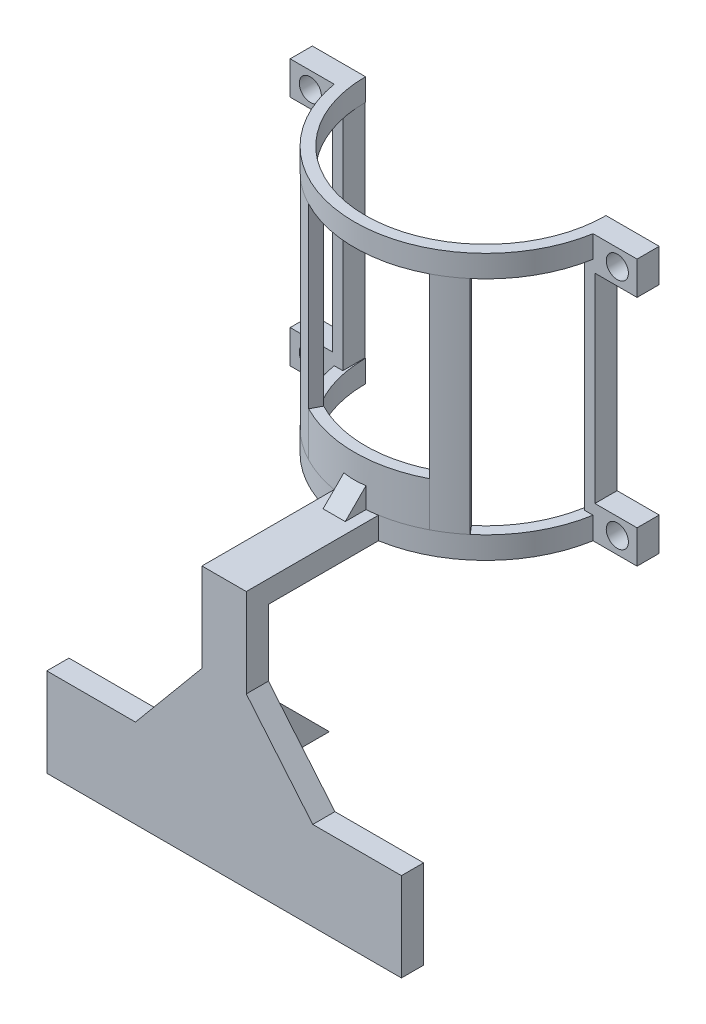
SolidWorks part; units mm, degrees
ref_plane "前视基准面" through (0, 0, 0) normal (0, 0, 1) x (1, 0, 0)
ref_plane "上视基准面" through (0, 0, 0) normal (0, 1, 0) x (1, 0, 0)
ref_plane "右视基准面" through (0, 0, 0) normal (1, 0, 0) x (0, 0, -1)
sketch "草图1" plane through (0, 0, 0) normal (0, 1, 0) x (1, 0, 0)
  line L0 (-118.5, 0) -> (-108.5, 0)
  line L1 (108.5, 0) -> (118.5, 0)
  arc A1 (-118.5, 0) -> (118.5, 0) centre (0, 0) ccw
  arc A2 (-108.5, 0) -> (108.5, 0) centre (0, 0) ccw
extrude "凸台-拉伸1" add sketch "草图1" along normal blind 20
ref_plane "基准面1" through (0, 0, 216.11) normal (0, 0, 1) x (1, 0, 0)
sketch "草图3" plane through (0, 0, 216.11) normal (0, 0, 1) x (1, 0, 0)
  line L0 (0, 0) -> (20, 0)
  line L2 (-118.5, 0) -> (118.5, 0) construction
  line L4 (20, 0) -> (20, 20)
  line L5 (118.5, 20) -> (-118.5, 20) construction
  line L6 (20, 20) -> (-20, 20)
  line L7 (-20, 20) -> (-20, 0)
  line L8 (-20, 0) -> (0, 0)
extrude "凸台-拉伸2" add sketch "草图3" against normal up to next
sketch "草图12" plane through (0, 0, 0) normal (0, 0, 1) x (1, 0, 0)
  line L0 (-109, 0) -> (-156.5, 0)
  line L1 (-156.5, 0) -> (-156.5, 30)
  line L2 (-156.5, 30) -> (-118.5, 30)
  line L3 (-109, 240) -> (-109, 0)
  line L4 (-109, 240) -> (-156.5, 240)
  line L5 (-156.5, 240) -> (-156.5, 210)
  line L6 (-118.5, 30) -> (-118.5, 210)
  line L7 (-118.5, 210) -> (-156.5, 210)
  line L8 (156.5, 0) -> (109, 0)
  line L10 (156.5, 0) -> (156.5, 30)
  line L11 (156.5, 30) -> (118.5, 30)
  line L12 (118.5, 30) -> (118.5, 210)
  line L13 (118.5, 210) -> (156.5, 210)
  line L14 (156.5, 210) -> (156.5, 240)
  line L15 (156.5, 240) -> (109, 240)
  line L17 (109, 240) -> (109, 0)
extrude "凸台-拉伸7" add sketch "草图12" along normal blind 20
sketch "草图13" plane through (0, 0, 0) normal (0, 0, -1) x (-1, 0, 0)
  line L0 (-156.5, 30) -> (-118.5, 30) construction
  line L1 (-156.5, 0) -> (-108.5, 0) construction
  line L2 (-118.5, 210) -> (-156.5, 210) construction
  line L3 (118.5, 30) -> (156.5, 30) construction
  line L4 (109, 240) -> (156.5, 240) construction
  line L6 (156.5, 240) -> (156.5, 210) construction
  line L7 (156.5, 30) -> (156.5, 0) construction
  circle A0 centre (138.3061, 225) radius 10
  circle A1 centre (138.3061, 15) radius 10
  circle A2 centre (-138.7046, 225) radius 10
  circle A3 centre (-138.7046, 15) radius 10
  point P12 (-138.7887, 0)
  point P19 (0, 0)
  point P21 (156.5, 219.3851)
  dimension "D1" = 30
  dimension "D2" = 20
  dimension "D3" = 15
  dimension "D4" = 15
  dimension "D5" = 15
  dimension "D6" = 15
  dimension "D7" = 18.1939
  dimension "D8" = 18.1939
extrude "切除-拉伸1" cut sketch "草图13" against normal blind 20
sketch "草图14" plane through (0, 240, 0) normal (0, 1, 0) x (1, 0, 0)
  line L0 (-58.5491, 0) -> (59.2996, 0) construction
  line L1 (0, 31.5353) -> (0, -144.5636) construction
  line L2 (-118.5, 0) -> (-108.5, 0)
  line L3 (108.5, 0) -> (118.5, 0)
  arc A0 (-108.5, 0) -> (108.5, 0) centre (0, 0) ccw
  arc A1 (-108.5, 0) -> (108.5, 0) centre (0, 0) ccw construction
  arc A2 (118.5, 0) -> (-118.5, 0) centre (0, 0) cw
  dimension "D1" = 108.5
  dimension "D2" = 118.5
extrude "凸台-拉伸8" add sketch "草图14" against normal blind 20
sketch "草图15" plane through (0, 220, 0) normal (0, -1, 0) x (1, 0, 0)
  line L0 (54.6083, 105.1674) -> (50, 96.2925)
  line L1 (76.4516, 90.5395) -> (70, 82.899)
  line L2 (-76.4516, 90.5395) -> (-70, 82.899)
  line L3 (0, 101.3639) -> (0, -9.7921) construction
  line L4 (-54.6083, 105.1674) -> (-50, 96.2925)
  arc A0 (54.6083, 105.1674) -> (76.4516, 90.5395) centre (0.0001, 0.0002) cw
  arc A1 (116.8, 20) -> (20, 116.8) centre (0, 0) ccw construction
  arc A2 (108.5, 0) -> (-108.5, 0) centre (0, 0) ccw construction
  arc A3 (50, 96.2925) -> (70, 82.899) centre (0, 0) cw
  arc A4 (-50, 96.2925) -> (-70, 82.899) centre (0, 0) ccw
  arc A5 (-54.6083, 105.1674) -> (-76.4516, 90.5395) centre (-0.0001, 0.0002) ccw
  dimension "D1" = 50
  dimension "D2" = 70
extrude "凸台-拉伸9" add sketch "草图15" along normal blind 200
sketch "草图16" plane through (0, 20, 0) normal (0, 1, 0) x (1, 0, 0)
  line L0 (-50, -96.2925) -> (-54.6083, -105.1674)
  line L1 (50, -96.2925) -> (54.6083, -105.1674)
  arc A0 (-50, -96.2925) -> (50, -96.2925) centre (0, 0) ccw
  arc A1 (-54.6083, -105.1674) -> (54.6083, -105.1674) centre (0, 0.0001) ccw
extrude "凸台-拉伸10" add sketch "草图16" along normal blind 40
sketch "草图17" plane through (0, 0, 0) normal (1, 0, 0) x (0, 0, -1)
  line L0 (-136.8, 20) -> (-116.8, 20)
  line L1 (-116.8, 20) -> (-216.11, 20) construction
  line L2 (-116.8, 20) -> (-116.8, 40)
  line L3 (-116.8, 40) -> (-136.8, 20)
  dimension "D1" = 20
  dimension "D2" = 20
extrude "凸台-拉伸11" add sketch "草图17" along normal mid plane 20
sketch "草图18" plane through (0, 0, 216.11) normal (0, 0, 1) x (1, 0, 0)
  line L0 (-20, 20) -> (20, 20)
  line L1 (20, 20) -> (20, 0)
  line L2 (20, 0) -> (20, -60)
  line L3 (20, -60) -> (80, -132)
  line L4 (80, -132) -> (160, -132)
  line L5 (160, -132) -> (160, -212)
  line L6 (160, -212) -> (-160, -212)
  line L7 (0, -126.2401) -> (0, 33.8738) construction
  line L8 (-160, -132) -> (-160, -212)
  line L9 (-80, -132) -> (-160, -132)
  line L10 (-20, -60) -> (-80, -132)
  line L11 (-20, 0) -> (-20, -60)
  line L12 (-20, 0) -> (-20, 20)
  point P15 (0, -212)
  dimension "D1" = 320
  dimension "D2" = 60
  dimension "D3" = 80
  dimension "D4" = 72
  dimension "D5" = 60
extrude "凸台-拉伸13" add sketch "草图18" along normal blind 20
sketch "草图22" plane through (0, 0, 0) normal (1, 0, 0) x (0, 0, -1)
  line L0 (-216.11, -72) -> (-156.11, -132)
  line L1 (-216.11, 176) -> (-216.11, -176) construction
  line L2 (-156.11, -132) -> (-216.11, -132)
  line L3 (-216.11, -132) -> (-216.11, -72)
  line L4 (-116.8, 0) -> (-216.11, 0) construction
  dimension "D1" = 132
  dimension "D2" = 132
  dimension "D3" = 60
  dimension "D4" = 60
extrude "凸台-拉伸14" add sketch "草图22" along normal mid plane 30
